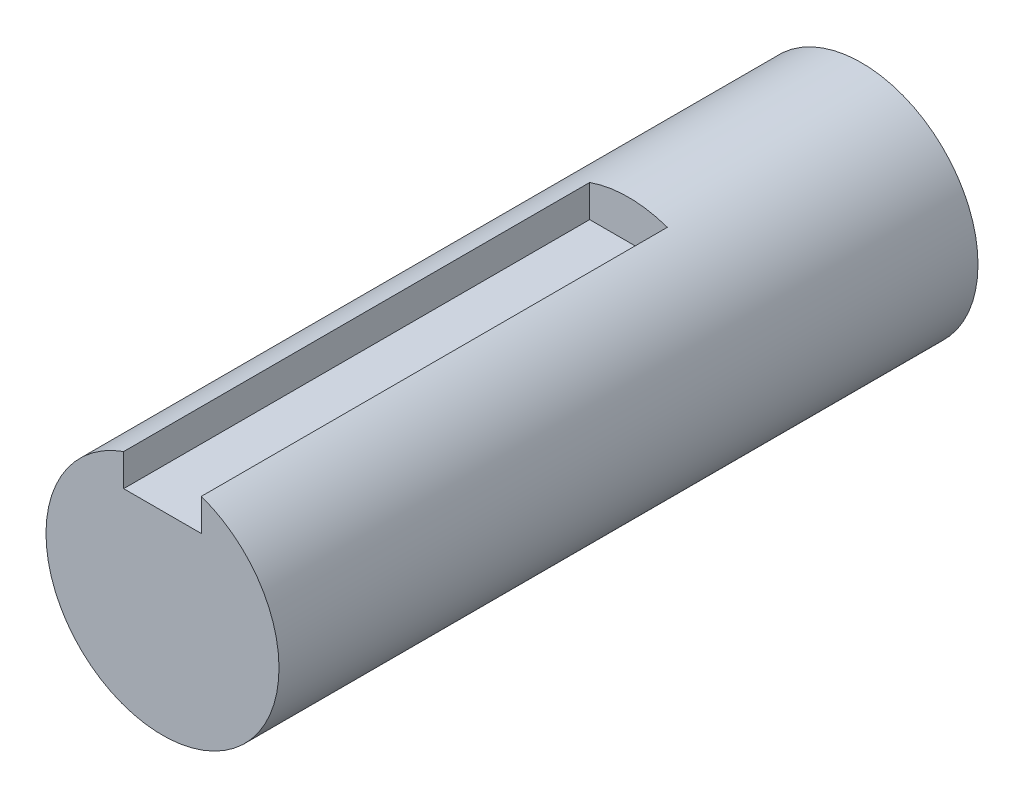
SolidWorks part; units mm, degrees
ref_plane "Front Plane" through (0, 0, 0) normal (0, 0, 1) x (1, 0, 0)
ref_plane "Top Plane" through (0, 0, 0) normal (0, 1, 0) x (1, 0, 0)
ref_plane "Right Plane" through (0, 0, 0) normal (1, 0, 0) x (0, 0, -1)
sketch "Sketch1" plane through (0, 0, 0) normal (0, 0, 1) x (1, 0, 0)
  circle A0 centre (0, 0) radius 7.5
  dimension "D1" = 15
extrude "Boss-Extrude1" add sketch "Sketch1" along normal blind 45
sketch "Sketch2" plane through (0, 0, 45) normal (0, 0, 1) x (1, 0, 0)
  line L1 (-2.5, 5) -> (2.5, 5)
  line L2 (-2.5, 5) -> (-2.5, 9.46)
  line L3 (-2.5, 9.46) -> (2.5, 9.46)
  line L4 (2.5, 5) -> (2.5, 9.46)
  line L5 (-2.5, 5) -> (2.5, 9.46) construction
  line L6 (-2.5, 9.46) -> (2.5, 5) construction
  point P0 (0, 7.23)
  point P5 (0, 5)
  dimension "D1" = 5
  dimension "D2" = 5
extrude "Cut-Extrude1" cut sketch "Sketch2" against normal blind 30
